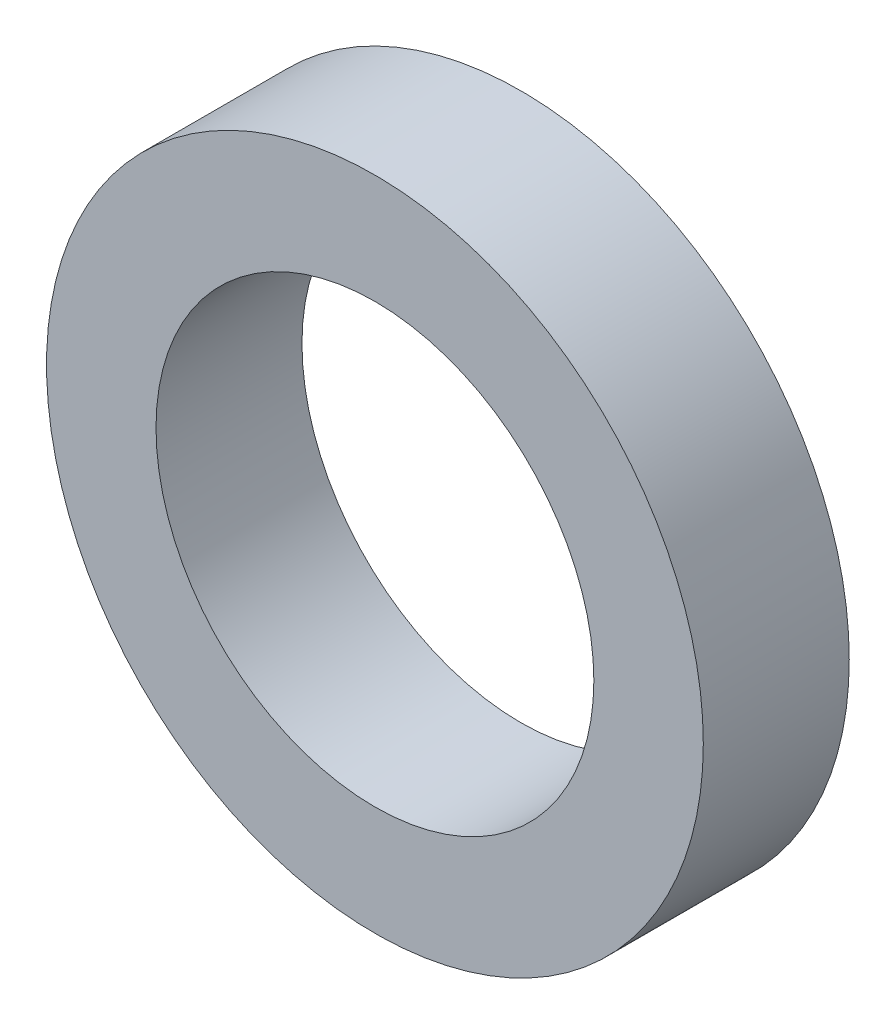
SolidWorks part; units mm, degrees
ref_plane "前视基准面" through (0, 0, 0) normal (0, 0, 1) x (1, 0, 0)
ref_plane "上视基准面" through (0, 0, 0) normal (0, 1, 0) x (1, 0, 0)
ref_plane "右视基准面" through (0, 0, 0) normal (1, 0, 0) x (0, 0, -1)
sketch "草图1" plane through (0, 0, 0) normal (0, 0, 1) x (1, 0, 0)
  circle A0 centre (0, 0) radius 6
  circle A1 centre (0, 0) radius 9
  dimension "D1" = 18
  dimension "D2" = 12
extrude "凸台-拉伸1" add sketch "草图1" along normal blind 4
